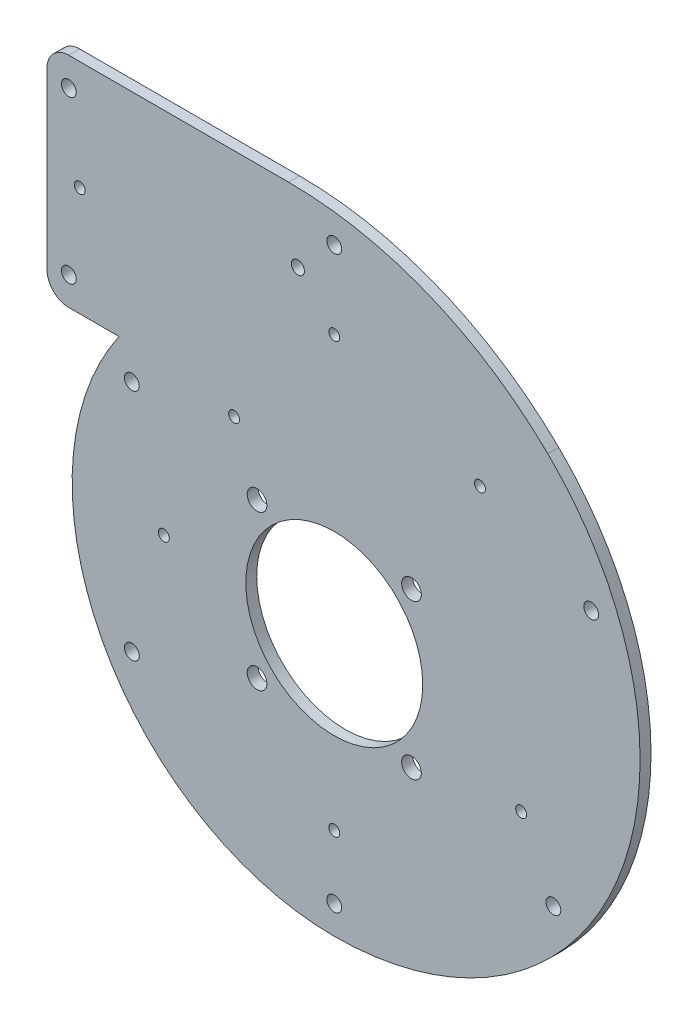
SolidWorks part; units mm, degrees
ref_plane "Plan de face" through (0, 0, 0) normal (0, 0, 1) x (1, 0, 0)
ref_plane "Plan de dessus" through (0, 0, 0) normal (0, 1, 0) x (1, 0, 0)
ref_plane "Plan de droite" through (0, 0, 0) normal (1, 0, 0) x (0, 0, -1)
sketch "Esquisse1" plane through (0, 0, 0) normal (0, 0, 1) x (1, 0, 0)
  line L0 (-100, 0) -> (0, 0) construction
  line L1 (0, 0) -> (0, -100) construction
  line L2 (-20.9527, 148.5294) -> (-146.5032, 148.5294) construction
  line L3 (-46.5032, 88.5294) -> (-146.5032, 88.5294) construction
  line L4 (-146.5032, 148.5294) -> (-146.5032, 88.5294) construction
  line L5 (-146.5032, 148.5294) -> (-146.5032, 88.5294) construction
  line L6 (-98.5075, 68.5294) -> (-146.5032, 68.5294)
  line L7 (-98.5075, 68.5294) -> (-166.5032, 68.5294) construction
  line L8 (-20.9527, 168.5294) -> (-146.5032, 168.5294)
  line L9 (-146.5032, 168.5294) -> (-146.5032, 68.5294)
  line L11 (-20.9527, 168.5294) -> (-166.5032, 168.5294) construction
  line L12 (-166.5032, 168.5294) -> (-166.5032, 68.5294) construction
  arc A0 (-100, 0) -> (0, -100) centre (0, 0) ccw construction
  arc A1 (0, -100) -> (83.8106, 105.8824) centre (0, 20) ccw construction
  arc A2 (83.8106, 105.8824) -> (-20.9527, 148.5294) centre (-20.9527, -1.4706) ccw construction
  arc A3 (-100, 0) -> (-46.5032, 88.5294) centre (0, 0) cw construction
  arc A4 (97.7791, 120.1961) -> (-20.9527, 168.5294) centre (-20.9527, -1.4706) ccw
  arc A5 (0, -120) -> (97.7791, 120.1961) centre (0, 20) ccw
  arc A6 (-120, 0) -> (0, -120) centre (0, 0) ccw
  arc A7 (-120, 0) -> (-98.5075, 68.5294) centre (0, 0) cw
  point P25 (-146.5032, 148.5294)
  dimension "D1" = 100
  dimension "D2" = 120
  dimension "D3" = 150
  dimension "D4" = 150
  dimension "D5" = 60
  dimension "D6" = 100
extrude "Boss.-Extru.1" add sketch "Esquisse1" along normal blind 5
sketch "Esquisse11" plane through (0, 0, 5) normal (0, 0, 1) x (1, 0, 0)
  line L0 (0, 0) -> (70.2748, 70.2748) construction
  line L1 (0, 0) -> (0, 185.3273) construction
  circle A0 centre (0, 0) radius 50 construction
  circle A1 centre (35.3553, 35.3553) radius 4.5
  dimension "D1" = 100
  dimension "D3" = 9
  dimension "D4" = 100
  dimension "D2" = 45
extrude "Enlèv. mat.-Extru.7" cut sketch "Esquisse11" against normal blind 13
sketch "Esquisse2" plane through (0, 0, 5) normal (0, 0, 1) x (1, 0, 0)
  circle A0 centre (0, 0) radius 40.5
  dimension "D1" = 81
sketch "Esquisse8" plane through (0, 0, 5) normal (0, 0, 1) x (1, 0, 0)
  line L0 (-46.5032, 88.5294) -> (-146.5032, 88.5294)
  line L1 (-146.5032, 88.5294) -> (-146.5032, 148.5294)
  line L2 (-146.5032, 148.5294) -> (-20.9527, 148.5294)
  line L3 (-148.5032, 150.5294) -> (-20.9527, 150.5294)
  line L4 (-148.5032, 86.5294) -> (-148.5032, 150.5294)
  line L5 (-54.0061, 86.5294) -> (-148.5032, 86.5294)
  arc A0 (-46.5032, 88.5294) -> (0, -100) centre (0, 0) ccw
  arc A1 (0, -100) -> (83.8106, 105.8824) centre (0, 20) ccw
  arc A2 (83.8106, 105.8824) -> (-20.9527, 148.5294) centre (-20.9527, -1.4706) ccw
  arc A3 (-54.0061, 86.5294) -> (0, -102) centre (0, 0) ccw
  arc A4 (0, -102) -> (85.2075, 107.3137) centre (0, 20) ccw
  arc A5 (85.2075, 107.3137) -> (-20.9527, 150.5294) centre (-20.9527, -1.4706) ccw
  dimension "D1" = 200
  dimension "D2" = 240
  dimension "D3" = 300
extrude "Enlèv. mat.-Extru.5" cut sketch "Esquisse8" against normal blind 0.2
extrude "Enlèv. mat.-Extru.1" cut sketch "Esquisse2" against normal blind 10
sketch "Esquisse3" plane through (0, 0, 0) normal (0, 0, -1) x (-1, 0, 0)
  circle A0 centre (16.656, 136.8684) radius 3
extrude "Enlèv. mat.-Extru.2" cut sketch "Esquisse3" against normal through all
sketch "Esquisse10" plane through (0, 0, 5) normal (0, 0, 1) x (1, 0, 0)
  line L5 (0, 0) -> (0, 188.8633) construction
  line L6 (0, 0) -> (163.5605, 94.4317) construction
  line L7 (-20.9527, 155.5294) -> (-146.5032, 155.5294)
  line L8 (-146.5032, 81.5294) -> (-69.2961, 81.5294)
  line L9 (-20.9527, 155.5294) -> (-146.5032, 155.5294) construction
  line L10 (-146.5032, 81.5294) -> (-69.2961, 81.5294) construction
  line L11 (0, 0) -> (163.5605, -94.4317) construction
  line L12 (0, 0) -> (0, -188.8633) construction
  line L13 (0, 0) -> (-163.5605, -94.4317) construction
  line L14 (0, 0) -> (-163.5605, 94.4317) construction
  line L15 (-121.5032, 201.3903) -> (-121.5032, 45.1866) construction
  circle A0 centre (-121.5032, 155.5294) radius 3.4
  circle A1 centre (117.6178, 67.9067) radius 3.4
  circle A2 centre (100.2973, -57.9067) radius 3.4
  circle A3 centre (0, -107) radius 3.4
  circle A4 centre (-92.6647, -53.5) radius 3.4
  circle A5 centre (-92.6647, 53.5) radius 3.4
  circle A7 centre (-121.5032, 81.5294) radius 3.4
  circle A10 centre (0, 154.125) radius 3.4
  arc A13 (88.6996, 110.8922) -> (-20.9527, 155.5294) centre (-20.9527, -1.4706) ccw
  arc A14 (0, -107) -> (88.6996, 110.8922) centre (0, 20) ccw
  arc A15 (-69.2961, 81.5294) -> (0, -107) centre (0, 0) ccw
  arc A16 (88.6996, 110.8922) -> (-20.9527, 155.5294) centre (-20.9527, -1.4706) ccw construction
  arc A17 (0, -107) -> (88.6996, 110.8922) centre (0, 20) ccw construction
  arc A18 (-69.2961, 81.5294) -> (0, -107) centre (0, 0) ccw construction
  point P9 (0, 0)
  dimension "D3" = 6.8
  dimension "D11" = 6.8
  dimension "D2" = 6
  dimension "D4" = 25
  dimension "D1" = 5
extrude "Enlèv. mat.-Extru.6" cut sketch "Esquisse10" against normal blind 13 contours A0 | A10 | A1 | A2 | A3 | A4 | A5 | A7
pattern_circular "Répétition circulaire1" count 4 over 360 about axis through (0, 0, 0) along (0, 0, 1) of "Enlèv. mat.-Extru.7"
sketch "Esquisse4" plane through (0, 0, 5) normal (0, 0, 1) x (1, 0, 0)
  line L0 (-88.257, 25.531) -> (-69.5459, -24.3356)
  line L1 (-69.5459, -24.3356) -> (-54.2661, -21.5826)
  line L2 (-54.2661, -21.5826) -> (-54.2661, 31.2111)
  line L3 (-54.2661, 31.2111) -> (-88.257, 25.531)
extrude "Enlèv. mat.-Extru.3" [suppressed] cut sketch "Esquisse4" against normal blind 274
sketch "Esquisse12" [suppressed] plane through (0, 0, 0) normal (0, 0, -1) x (-1, 0, 0)
  line L0 (46.5032, 88.5294) -> (146.5032, 88.5294)
  line L2 (146.5032, 148.5294) -> (20.9527, 148.5294)
  line L3 (146.5032, 150.5294) -> (20.9527, 150.5294)
  line L4 (54.0061, 86.5294) -> (146.5032, 86.5294)
  line L5 (146.5032, 148.5294) -> (146.5032, 88.5294)
  line L6 (146.5032, 150.5294) -> (148.5032, 150.5294)
  line L7 (148.5032, 150.5294) -> (148.5032, 86.5294)
  line L8 (148.5032, 86.5294) -> (146.5032, 86.5294)
  arc A0 (0, -100) -> (46.5032, 88.5294) centre (0, 0) ccw
  arc A1 (20.9527, 148.5294) -> (-83.8106, 105.8824) centre (20.9527, -1.4706) ccw
  arc A2 (-83.8106, 105.8824) -> (0, -100) centre (0, 20) ccw
  arc A3 (20.9527, 150.5294) -> (-85.2075, 107.3137) centre (20.9527, -1.4706) ccw
  arc A4 (-85.2075, 107.3137) -> (0, -102) centre (0, 20) ccw
  arc A5 (0, -102) -> (54.0061, 86.5294) centre (0, 0) ccw
  dimension "D1" = 200
  dimension "D2" = 300
  dimension "D3" = 240
extrude "Enlèv. mat.-Extru.8" [suppressed] cut sketch "Esquisse12" against normal blind 0.2
sketch "Esquisse13" [suppressed] plane through (0, 0, 0) normal (0, 0, -1) x (-1, 0, 0)
  line L0 (0, 0) -> (0, 199.0737) construction
  line L1 (0, 0) -> (172.4029, 99.5369) construction
  line L2 (0, 0) -> (172.4029, -99.5369) construction
  line L3 (0, 0) -> (0, -199.0737) construction
  line L4 (0, 0) -> (-172.4029, -99.5369) construction
  line L5 (0, 0) -> (-172.4029, 99.5369) construction
  line L6 (146.5032, 155.5294) -> (20.9527, 155.5294)
  line L7 (146.5032, 155.5294) -> (20.9527, 155.5294) construction
  line L8 (121.5032, 199.4928) -> (121.5032, 58.0637) construction
  line L9 (146.5032, 148.5294) -> (146.5032, 88.5294) construction
  line L12 (54.0061, 81.5294) -> (146.5032, 81.5294)
  line L13 (54.0061, 81.5294) -> (146.5032, 81.5294) construction
  circle A0 centre (-117.6178, 67.9067) radius 4.25
  circle A1 centre (-100.2973, -57.9067) radius 4.25
  circle A2 centre (0, -107) radius 4.25
  circle A3 centre (92.6647, -53.5) radius 4.25
  circle A4 centre (92.6647, 53.5) radius 4.25
  circle A5 centre (121.5032, 155.5294) radius 4.25
  circle A6 centre (0, 154.125) radius 4.25
  circle A7 centre (121.5032, 81.5294) radius 4.25
  circle A8 centre (69.2961, 81.5294) radius 4.25
  arc A9 (0, -107) -> (56.6535, 90.771) centre (0, 0) ccw
  arc A10 (-88.6996, 110.8922) -> (0, -107) centre (0, 20) ccw
  arc A11 (20.9527, 155.5294) -> (-88.6996, 110.8922) centre (20.9527, -1.4706) ccw
  arc A12 (0, -107) -> (56.6535, 90.771) centre (0, 0) ccw construction
  arc A13 (-88.6996, 110.8922) -> (0, -107) centre (0, 20) ccw construction
  arc A14 (20.9527, 155.5294) -> (-88.6996, 110.8922) centre (20.9527, -1.4706) ccw construction
  point P25 (0, 0)
  dimension "D10" = 8.5
  dimension "D1" = 5
  dimension "D4" = 25
  dimension "D11" = 5
  dimension "D3" = 6
extrude "Enlèv. mat.-Extru.9" [suppressed] cut sketch "Esquisse13" against normal blind 10
sketch "Esquisse14" [suppressed] plane through (0, 0, 5) normal (0, 0, 1) x (1, 0, 0)
  line L1 (0, 0) -> (0, 45) construction
  line L2 (0, 0) -> (0, -45) construction
  line L3 (0, -45) -> (45, 0) construction
  line L4 (0, 45) -> (45, 0) construction
  line L5 (0, 0) -> (45, 0) construction
  line L6 (0, -45) -> (0, 45) construction
  circle A0 centre (0, 45) radius 6
  circle A1 centre (45, 0) radius 6 construction
  circle A2 centre (0, -45) radius 6
  circle A3 centre (-45, 0) radius 6 construction
  point P0 (0, 0)
  point P16 (0, 0)
  dimension "D1" = 12.2
  dimension "D2" = 4
  dimension "D3" = 90
extrude "Enlèv. mat.-Extru.10" [suppressed] cut sketch "Esquisse14" against normal blind 10
sketch "Esquisse15" plane through (0, 0, 5) normal (0, 0, 1) x (1, 0, 0)
  line L1 (-82, -50) -> (-32, -50)
  line L2 (-82, -50) -> (-82, 59)
  line L3 (-82, 59) -> (-32, 59)
  line L4 (-32, -50) -> (-32, 59)
  point P7 (-32, 4.5)
  dimension "D1" = 50
  dimension "D2" = 109
  dimension "D3" = 32
  dimension "D4" = 4.5
extrude "Enlèv. mat.-Extru.11" [suppressed] cut sketch "Esquisse15" against normal through all
sketch "Esquisse16" [suppressed] plane through (0, 0, 5) normal (0, 0, 1) x (1, 0, 0)
  line L0 (-32, -50) -> (-32, 59) construction
  line L2 (-32, -50) -> (-32, 59)
  line L3 (-82, 59) -> (-82, -50)
sketch "Esquisse20" plane through (0, 0, 0) normal (0, 0, -1) x (-1, 0, 0)
  line L0 (-50, -147.5) -> (-50, -157.5) construction
  line L1 (-65, -100.8712) -> (65, -100.8712)
  line L2 (-65, -100.8712) -> (-65, -170)
  line L3 (-65, -170) -> (65, -170)
  line L4 (65, -100.8712) -> (65, -170)
  line L9 (-44.5, -147.5) -> (-44.5, -157.5)
  line L10 (-55.5, -147.5) -> (-55.5, -157.5)
  line L11 (50, -147.5) -> (50, -157.5) construction
  line L12 (55.5, -147.5) -> (55.5, -157.5)
  line L13 (44.5, -147.5) -> (44.5, -157.5)
  line L15 (50, -152.5) -> (-50, -152.5) construction
  arc A0 (-97.7791, 120.1961) -> (0, -120) centre (0, 20) ccw construction
  arc A2 (-44.5, -147.5) -> (-55.5, -147.5) centre (-50, -147.5) ccw
  arc A3 (-55.5, -157.5) -> (-44.5, -157.5) centre (-50, -157.5) ccw
  arc A4 (55.5, -147.5) -> (44.5, -147.5) centre (50, -147.5) ccw
  arc A5 (44.5, -157.5) -> (55.5, -157.5) centre (50, -157.5) ccw
  arc A6 (0, -120) -> (98.5075, 68.5294) centre (0, 0) ccw construction
  point P7 (0, -152.5)
  point P16 (-50, -152.5)
  point P21 (50, -152.5)
  point P30 (0, -170)
  dimension "D2" = 50
  dimension "D5" = 11
  dimension "D1" = 130
  dimension "D3" = 100
  dimension "D4" = 17.5
  dimension "D6" = 10
extrude "Boss.-Extru.2" [suppressed] add sketch "Esquisse20" against normal blind 5
fillet "Congé1" [suppressed] radius 10
sketch "Esquisse21" [suppressed] plane through (0, 0, 5) normal (0, 0, 1) x (1, 0, 0)
  line L0 (115.54, -130) -> (88.54, -130) construction
  line L1 (-77.46, -130) -> (-104.46, -130) construction
  line L2 (115.54, -130) -> (88.54, -130)
  line L3 (-77.46, -130) -> (-104.46, -130)
ref_plane "Plan3" [suppressed] through (0, 0, 2.5) normal (0, 0, 1) x (1, 0, 0)
sketch "Esquisse24" plane through (0, 0, 5) normal (0, 0, 1) x (1, 0, 0)
  line L6 (-146.5032, 150.5294) -> (-146.5032, 148.5294)
  line L7 (-146.5032, 148.5294) -> (-20.9527, 148.5294)
  line L8 (-46.5032, 88.5294) -> (-146.5032, 88.5294)
  line L9 (-146.5032, 88.5294) -> (-146.5032, 86.5294)
  line L10 (-146.5032, 86.5294) -> (-54.0061, 86.5294)
  line L11 (-20.9527, 150.5294) -> (-146.5032, 150.5294)
  line L12 (-146.5032, 150.5294) -> (-146.5032, 148.5294)
  line L13 (-146.5032, 148.5294) -> (-20.9527, 148.5294)
  line L14 (-46.5032, 88.5294) -> (-146.5032, 88.5294)
  line L15 (-146.5032, 88.5294) -> (-146.5032, 86.5294)
  line L16 (-146.5032, 86.5294) -> (-54.0061, 86.5294)
  line L17 (-20.9527, 150.5294) -> (-146.5032, 150.5294)
  arc A6 (83.8106, 105.8824) -> (-20.9527, 148.5294) centre (-20.9527, -1.4706) ccw
  arc A7 (0, -100) -> (83.8106, 105.8824) centre (0, 20) ccw
  arc A8 (-46.5032, 88.5294) -> (0, -100) centre (0, 0) ccw
  arc A9 (-54.0061, 86.5294) -> (0, -102) centre (0, 0) ccw
  arc A10 (0, -102) -> (85.2075, 107.3137) centre (0, 20) ccw
  arc A11 (85.2075, 107.3137) -> (-20.9527, 150.5294) centre (-20.9527, -1.4706) ccw
  arc A12 (83.8106, 105.8824) -> (-20.9527, 148.5294) centre (-20.9527, -1.4706) ccw
  arc A13 (0, -100) -> (83.8106, 105.8824) centre (0, 20) ccw
  arc A14 (-46.5032, 88.5294) -> (0, -100) centre (0, 0) ccw
  arc A15 (-54.0061, 86.5294) -> (0, -102) centre (0, 0) ccw
  arc A16 (0, -102) -> (85.2075, 107.3137) centre (0, 20) ccw
  arc A17 (85.2075, 107.3137) -> (-20.9527, 150.5294) centre (-20.9527, -1.4706) ccw
  dimension "D1" = 0
extrude "Boss.-Extru.3" add sketch "Esquisse24" against normal up to vertex (0.2 mm away) up to point (-146.5032, 148.5294, 4.8)
sketch "Esquisse25" [suppressed] plane through (0, 0, 0) normal (0, 0, -1) x (-1, 0, 0)
  line L4 (146.5032, 86.5294) -> (146.5032, 88.5294)
  line L8 (20.9527, 148.5294) -> (146.5032, 148.5294)
  line L9 (146.5032, 148.5294) -> (146.5032, 150.5294)
  line L10 (146.5032, 150.5294) -> (20.9527, 150.5294)
  line L14 (20.9527, 148.5294) -> (146.5032, 148.5294)
  line L15 (146.5032, 148.5294) -> (146.5032, 150.5294)
  line L16 (146.5032, 150.5294) -> (20.9527, 150.5294)
  line L20 (146.5032, 86.5294) -> (146.5032, 88.5294)
  line L22 (146.5032, 88.5294) -> (46.5032, 88.5294)
  line L23 (146.5032, 88.5294) -> (46.5032, 88.5294)
  line L24 (54.0061, 86.5294) -> (146.5032, 86.5294)
  line L25 (54.0061, 86.5294) -> (146.5032, 86.5294)
  line L28 (82, 59) -> (82, 57.2364)
  line L29 (82, 59) -> (82, 57.2364)
  line L30 (80.7403, 59) -> (82, 59)
  line L31 (80.7403, 59) -> (82, 59)
  arc A6 (80.7403, 59) -> (46.5032, 88.5294) centre (0, 0) ccw
  arc A7 (-83.8106, 105.8824) -> (0, -100) centre (0, 20) ccw
  arc A8 (20.9527, 148.5294) -> (-83.8106, 105.8824) centre (20.9527, -1.4706) ccw
  arc A9 (20.9527, 150.5294) -> (-85.2075, 107.3137) centre (20.9527, -1.4706) ccw
  arc A10 (-85.2075, 107.3137) -> (0, -102) centre (0, 20) ccw
  arc A11 (0, -102) -> (54.0061, 86.5294) centre (0, 0) ccw
  arc A13 (-83.8106, 105.8824) -> (0, -100) centre (0, 20) ccw
  arc A14 (20.9527, 148.5294) -> (-83.8106, 105.8824) centre (20.9527, -1.4706) ccw
  arc A15 (20.9527, 150.5294) -> (-85.2075, 107.3137) centre (20.9527, -1.4706) ccw
  arc A16 (-85.2075, 107.3137) -> (0, -102) centre (0, 20) ccw
  arc A17 (0, -102) -> (54.0061, 86.5294) centre (0, 0) ccw
  arc A21 (80.7403, 59) -> (46.5032, 88.5294) centre (0, 0) ccw
  arc A23 (0, -100) -> (82, 57.2364) centre (0, 0) ccw
  arc A24 (0, -100) -> (82, 57.2364) centre (0, 0) ccw
  dimension "D1" = 0
extrude "Boss.-Extru.4" [suppressed] add sketch "Esquisse25" against normal up to vertex
sketch "Esquisse26" plane through (0, 0, 5) normal (0, 0, 1) x (1, 0, 0)
  line L0 (-146.5032, 68.5294) -> (-98.5075, 68.5294) construction
  line L1 (-146.5032, 168.5294) -> (-131.5032, 168.5294)
  line L2 (-146.5032, 168.5294) -> (-146.5032, 68.5294)
  line L3 (-146.5032, 68.5294) -> (-131.5032, 68.5294)
  line L4 (-131.5032, 168.5294) -> (-131.5032, 68.5294)
  dimension "D1" = 15
extrude "Enlèv. mat.-Extru.14" cut sketch "Esquisse26" against normal blind 10
fillet "Congé2" radius 10 2 edges at (-131.5032, 68.5294, 2.5) (-131.5032, 168.5294, 2.5)
sketch "Esquisse27" plane through (0, 0, 5) normal (0, 0, 1) x (1, 0, 0)
  line L0 (0, 0) -> (0, -100) construction
  line L1 (0, 0) -> (0, -130.2152) construction
  line L2 (0, 0) -> (-123.842, -40.2387) construction
  line L3 (0, 0) -> (-76.5386, 105.3463) construction
  line L4 (0, 0) -> (76.5386, 105.3463) construction
  line L5 (0, 0) -> (123.842, -40.2387) construction
  line L6 (0, 0) -> (0, 176.6739) construction
  line L7 (-131.5032, 118.5294) -> (0, 118.5294) construction
  line L8 (-131.5032, 78.5294) -> (-131.5032, 158.5294) construction
  circle A0 centre (-116.5032, 118.5294) radius 2.5
  circle A4 centre (0, 118.5294) radius 2.5
  circle A5 centre (66.7017, 91.807) radius 2.5
  circle A6 centre (85.5532, -27.7979) radius 2.5
  circle A7 centre (0, -78) radius 2.5
  arc A8 (68.4453, 90.1373) -> (-20.9527, 126.5294) centre (-20.9527, -1.4706) ccw
  arc A9 (0, -78) -> (68.4453, 90.1373) centre (0, 20) ccw
  arc A10 (-78, 0) -> (0, -78) centre (0, 0) ccw
  arc A11 (-36.2725, 69.0529) -> (-78, 0) centre (0, 0) ccw
  arc A12 (68.4453, 90.1373) -> (-20.9527, 126.5294) centre (-20.9527, -1.4706) ccw construction
  arc A13 (0, -78) -> (68.4453, 90.1373) centre (0, 20) ccw construction
  arc A14 (-78, 0) -> (0, -78) centre (0, 0) ccw construction
  arc A15 (-36.2725, 69.0529) -> (-78, 0) centre (0, 0) ccw construction
  circle A16 centre (-45.8472, 63.1033) radius 2.5
  circle A17 centre (-78, 0) radius 2.5
  point P8 (0, 0)
  dimension "D3" = 5
  dimension "D4" = 15
  dimension "D1" = 22
  dimension "D2" = 5
extrude "Enlèv. mat.-Extru.15" cut sketch "Esquisse27" against normal blind 10
